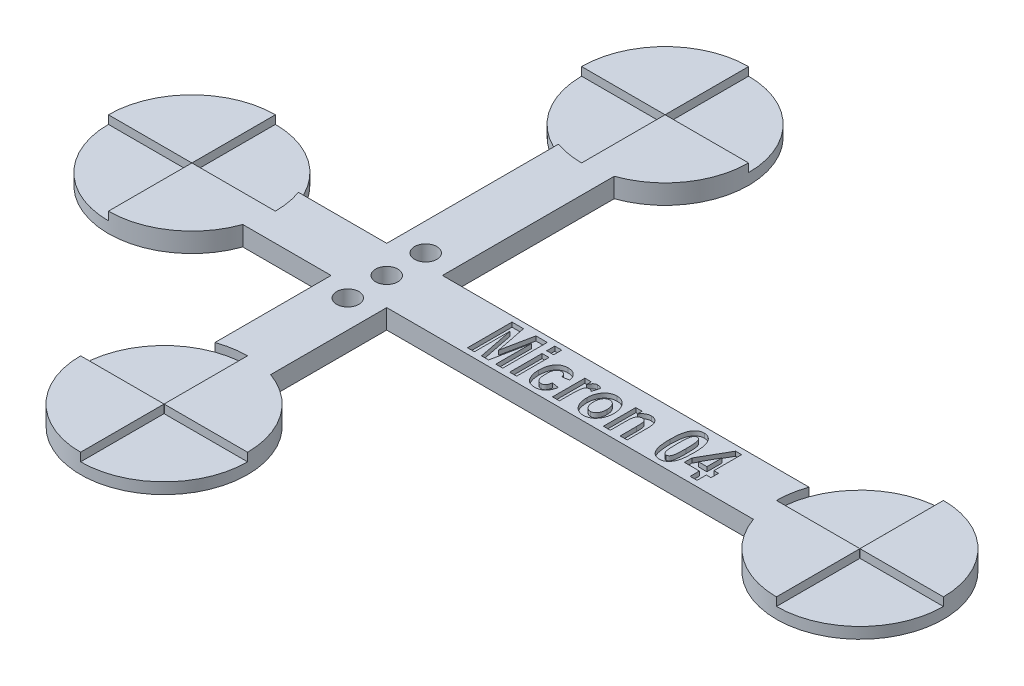
SolidWorks part; units mm, degrees
ref_plane "Front Plane" through (0, 0, 0) normal (0, 0, 1) x (1, 0, 0)
ref_plane "Top Plane" through (0, 0, 0) normal (0, 1, 0) x (1, 0, 0)
ref_plane "Right Plane" through (0, 0, 0) normal (1, 0, 0) x (0, 0, -1)
sketch "Sketch1" plane through (0, 0, 0) normal (0, 1, 0) x (1, 0, 0)
  line L0 (0, 0) -> (120, 0) construction
  line L1 (35, -40) -> (35, 50) construction
  line L2 (30, 35.8579) -> (30, 5)
  line L3 (40, -25.8579) -> (40, -5)
  line L4 (14.1421, 5) -> (30, 5)
  line L5 (105.8579, -5) -> (40, -5)
  line L6 (40, 5) -> (105.8579, 5)
  line L7 (30, -5) -> (30, -25.8579)
  line L8 (30, -5) -> (14.1421, -5)
  line L9 (40, 5) -> (40, 35.8579)
  arc A0 (14.1421, 5) -> (14.1421, -5) centre (0, 0) ccw
  arc A1 (105.8579, -5) -> (105.8579, 5) centre (120, 0) ccw
  arc A2 (40, 35.8579) -> (30, 35.8579) centre (35, 50) ccw
  arc A3 (30, -25.8579) -> (40, -25.8579) centre (35, -40) ccw
  dimension "D1" = 30
  dimension "D3" = 30
  dimension "D5" = 30
  dimension "D6" = 30
  dimension "D2" = 120
  dimension "D4" = 35
  dimension "D7" = 90
  dimension "D8" = 50
  dimension "D9" = 5
  dimension "D10" = 5
  dimension "D11" = 5
  dimension "D12" = 5
extrude "Boss-Extrude1" add sketch "Sketch1" along normal blind 3.5
sketch "Sketch2" plane through (0, 3.5, 0) normal (0, 1, 0) x (1, 0, 0)
  line L0 (-15, 0) -> (-0.05, 0)
  line L1 (35, 65) -> (35, 50.05)
  line L2 (20, 50) -> (34.95, 50)
  line L3 (120, 15) -> (120, 0.05)
  line L4 (0, 15) -> (0, 0.05)
  line L5 (20, -40) -> (34.95, -40)
  line L6 (35.05, 50) -> (50, 50)
  line L7 (35, 49.95) -> (35, 35)
  line L8 (35, -40.05) -> (35, -55)
  line L9 (35.05, -40) -> (50, -40)
  line L10 (0, -0.05) -> (0, -15)
  line L11 (0.05, 0) -> (15, 0)
  line L12 (120, -0.05) -> (120, -15)
  line L13 (120.05, 0) -> (135, 0)
  line L14 (105, 0) -> (119.95, 0)
  line L15 (35, -25) -> (35, -39.95)
  arc A0 (20, 50) -> (35, 35) centre (35, 50) ccw
  arc A1 (-15, 0) -> (0, -15) centre (0, 0) ccw
  arc A2 (35, -55) -> (50, -40) centre (35, -40) ccw
  arc A3 (120, 15) -> (105, 0) centre (120, 0) ccw
  arc A4 (0, 0.05) -> (-0.05, 0) centre (0, 0) ccw
  arc A5 (35, 49.95) -> (35.05, 50) centre (35, 50) ccw
  arc A6 (119.95, 0) -> (120, -0.05) centre (120, 0) ccw
  arc A7 (34.95, -40) -> (35, -40.05) centre (35, -40) ccw
  arc A8 (35, 50.05) -> (34.95, 50) centre (35, 50) ccw
  arc A9 (50, 50) -> (35, 65) centre (35, 50) ccw
  arc A10 (35.05, -40) -> (35, -39.95) centre (35, -40) ccw
  arc A11 (35, -25) -> (20, -40) centre (35, -40) ccw
  arc A12 (0, -0.05) -> (0.05, 0) centre (0, 0) ccw
  arc A13 (15, 0) -> (0, 15) centre (0, 0) ccw
  arc A14 (120.05, 0) -> (120, 0.05) centre (120, 0) ccw
  arc A15 (120, -15) -> (135, 0) centre (120, 0) ccw
  arc A16 (30, -25.8579) -> (40, -25.8579) centre (35, -40) ccw construction
  arc A17 (40, 35.8579) -> (30, 35.8579) centre (35, 50) ccw construction
  dimension "D1" = 0.1
  dimension "D2" = 0.1
  dimension "D3" = 0.1
  dimension "D4" = 0.1
extrude "Cut-Extrude1" cut sketch "Sketch2" against normal blind 1.5
sketch "Sketch3" plane through (0, 3.5, 0) normal (0, 1, 0) x (1, 0, 0)
  line L0 (50.4289, -4) -> (95.4289, -4) construction
  line L1 (40, -5) -> (105.8579, -5) construction
  text T0 "<b>Micron 04</b>" font "Arial Narrow" height 8
  point P4 (72.9289, -4)
  point P5 (72.9289, -5)
  dimension "D1" = 45
  dimension "D2" = 1
extrude "Cut-Extrude2" cut sketch "Sketch3" against normal blind 0.8
sketch "Sketch4" plane through (0, 3.5, 0) normal (0, 1, 0) x (1, 0, 0)
  line L0 (35, 7) -> (35, -7) construction
  line L1 (0.05, 0) -> (15, 0) construction
  line L2 (35, -39.95) -> (35, -25) construction
  circle A0 centre (35, 0) radius 2
  circle A1 centre (35, 7) radius 2
  circle A2 centre (35, -7) radius 2
  point P4 (35, 0)
  dimension "D1" = 4
  dimension "D3" = 4
  dimension "D4" = 4
  dimension "D2" = 14
extrude "Cut-Extrude3" cut sketch "Sketch4" against normal through all
